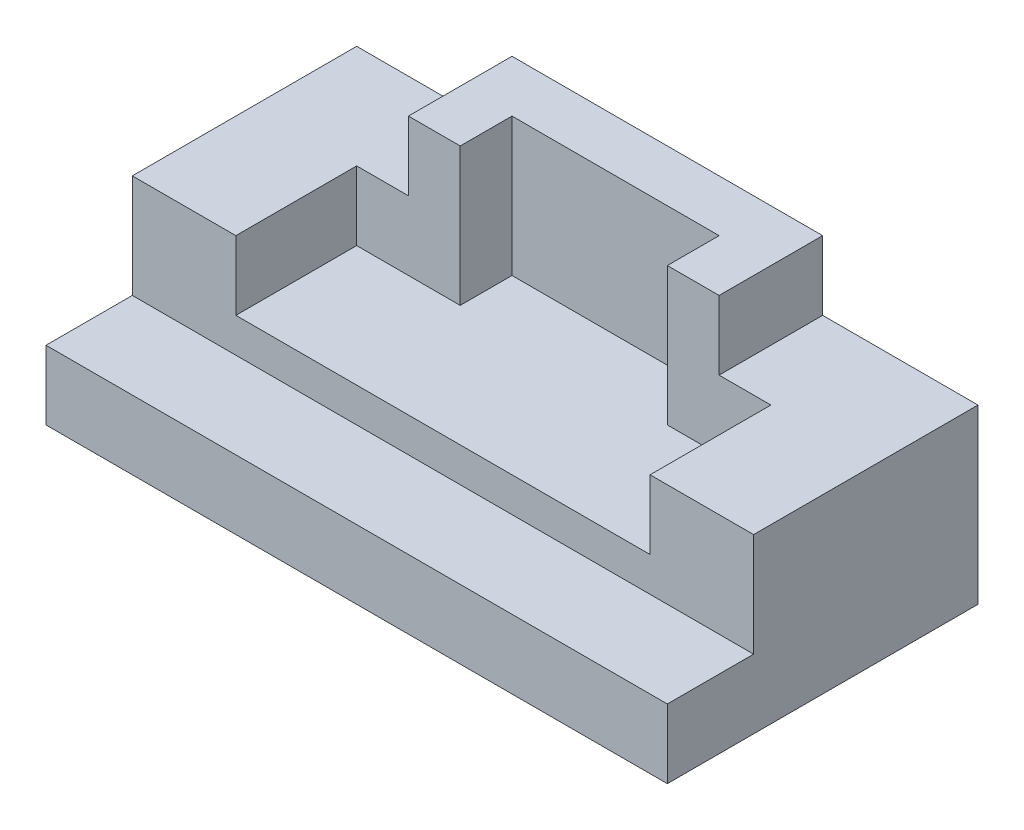
SolidWorks part; units mm, degrees
ref_plane "Front Plane" through (0, 0, 0) normal (0, 0, 1) x (1, 0, 0)
ref_plane "Top Plane" through (0, 0, 0) normal (0, 1, 0) x (1, 0, 0)
ref_plane "Right Plane" through (0, 0, 0) normal (1, 0, 0) x (0, 0, -1)
sketch "Sketch1" plane through (0, 0, 0) normal (1, 0, 0) x (0, 0, -1)
  line L0 (-28.575, 0) -> (28.575, 0)
  line L1 (28.575, 0) -> (28.575, 31.75)
  line L2 (28.575, 31.75) -> (-12.7, 31.75)
  line L3 (-12.7, 31.75) -> (-12.7, 12.7)
  line L4 (-12.7, 12.7) -> (-28.575, 12.7)
  line L5 (-28.575, 12.7) -> (-28.575, 0)
  dimension "D1" = 57.15
  dimension "D2" = 31.75
  dimension "D3" = 41.275
  dimension "D4" = 12.7
extrude "Boss-Extrude1" add sketch "Sketch1" along normal mid plane 114.3
sketch "Sketch2" plane through (0, 31.75, 0) normal (0, 1, 0) x (1, 0, 0)
  line L0 (-28.575, 28.575) -> (28.575, 28.575)
  line L1 (57.15, 28.575) -> (-57.15, 28.575) construction
  line L2 (28.575, 28.575) -> (28.575, 9.525)
  line L3 (28.575, 9.525) -> (19.05, 9.525)
  line L4 (19.05, 9.525) -> (19.05, 19.05)
  line L5 (19.05, 19.05) -> (-19.05, 19.05)
  line L6 (-19.05, 19.05) -> (-19.05, 9.525)
  line L7 (-19.05, 9.525) -> (-28.575, 9.525)
  line L8 (-28.575, 9.525) -> (-28.575, 28.575)
  line L11 (0, -17.4625) -> (0, 17.4625) construction
  point P9 (0, 28.575)
  dimension "D1" = 9.525
  dimension "D2" = 19.05
  dimension "D3" = 9.525
  dimension "D4" = 57.15
extrude "Boss-Extrude2" add sketch "Sketch2" along normal blind 12.7
sketch "Sketch3" plane through (0, 44.45, 0) normal (0, 1, 0) x (1, 0, 0)
  line L0 (-38.1, 9.525) -> (-19.05, 9.525)
  line L1 (38.1, 9.525) -> (38.1, -12.7)
  line L2 (57.15, -12.7) -> (-57.15, -12.7) construction
  line L3 (38.1, -12.7) -> (-38.1, -12.7)
  line L4 (57.15, -12.7) -> (-57.15, -12.7) construction
  line L5 (-38.1, -12.7) -> (-38.1, 9.525)
  line L6 (19.05, 9.525) -> (38.1, 9.525)
  line L7 (57.15, 28.575) -> (57.15, -12.7) construction
  line L8 (-19.05, 9.525) -> (-19.05, 19.05)
  line L9 (-19.05, 19.05) -> (19.05, 19.05)
  line L10 (19.05, 19.05) -> (19.05, 9.525)
  line L11 (19.05, 19.05) -> (19.05, 9.525) construction
  line L12 (19.05, 19.05) -> (19.05, 9.525) construction
  line L13 (0, -24.4475) -> (0, 24.4475) construction
  point P11 (0, 19.05)
  dimension "D1" = 19.05
extrude "Cut-Extrude1" cut sketch "Sketch3" against normal blind 25.4
